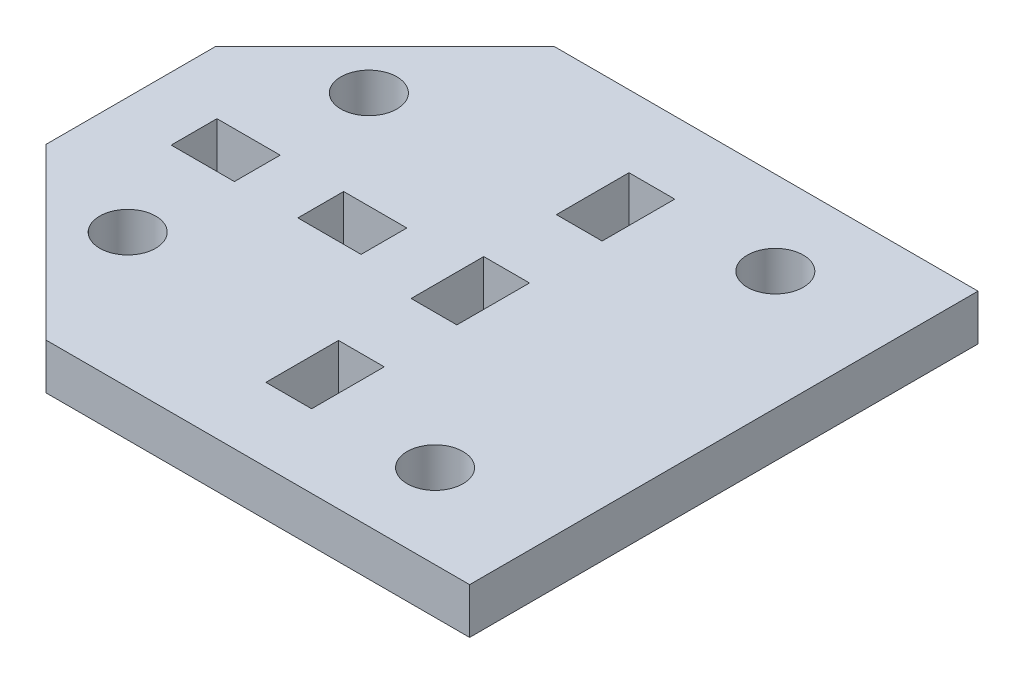
SolidWorks part; units mm, degrees
ref_plane "Ön Düzlem" through (0, 0, 0) normal (0, 0, 1) x (1, 0, 0)
ref_plane "Üst Düzlem" through (0, 0, 0) normal (0, 1, 0) x (1, 0, 0)
ref_plane "Sağ Düzlem" through (0, 0, 0) normal (1, 0, 0) x (0, 0, -1)
sketch "Sketch1" plane through (0, 0, 0) normal (0, 1, 0) x (1, 0, 0)
  line L0 (10.7767, -15.9461) -> (-9.2233, -15.9461)
  line L2 (10.7767, 14.0539) -> (-9.2233, 14.0539)
  line L4 (10.7767, -15.9461) -> (-9.2233, 14.0539) construction
  line L5 (10.7767, 14.0539) -> (-9.2233, -15.9461) construction
  line L14 (2.1267, -11.6204) -> (2.1267, -7.3347)
  line L16 (-19.2233, 4.0539) -> (-9.2233, 14.0539)
  line L17 (-9.2233, -15.9461) -> (-19.2233, -5.9461)
  line L18 (2.1267, -3.049) -> (2.1267, 1.2367)
  line L19 (-19.2233, 4.0539) -> (-19.2233, -5.9461)
  line L20 (2.1267, 5.5224) -> (2.1267, 9.8081)
  line L22 (-0.5733, -11.6204) -> (-0.5733, -7.3347)
  line L23 (10.7767, 14.0539) -> (15.7767, 14.0539)
  line L24 (-0.5733, -3.049) -> (-0.5733, 1.2367)
  line L26 (-0.5733, 5.5224) -> (-0.5733, 9.8081)
  line L27 (15.7767, 14.0539) -> (15.7767, -15.9461)
  line L28 (-0.5733, -11.6204) -> (2.1267, -11.6204)
  line L29 (-0.5733, -7.3347) -> (2.1267, -7.3347)
  line L30 (2.1267, -3.049) -> (-0.5733, -3.049)
  line L31 (-0.5733, 1.2367) -> (2.1267, 1.2367)
  line L32 (2.1267, 5.5224) -> (-0.5733, 5.5224)
  line L33 (-0.5733, 9.8081) -> (2.1267, 9.8081)
  line L34 (-15.4933, 0.4119) -> (-11.7633, 0.4119)
  line L35 (15.7767, -15.9461) -> (10.7767, -15.9461)
  line L36 (-8.0333, 0.4279) -> (-4.3033, 0.4279)
  line L38 (-15.4933, -2.2881) -> (-11.7633, -2.2881)
  line L40 (-8.0333, -2.2721) -> (-4.3033, -2.2721)
  line L42 (-15.4933, -2.2881) -> (-15.4933, 0.4119)
  line L43 (-11.7633, -2.2881) -> (-11.7633, 0.4119)
  line L44 (-8.0333, 0.4279) -> (-8.0333, -2.2721)
  line L45 (-4.3033, 0.4279) -> (-4.3033, -2.2721)
  circle A0 centre (-12.3262, -8.023) radius 1.65
  circle A2 centre (8.7767, 9.0938) radius 1.65
  circle A5 centre (-12.3262, 6.2107) radius 1.65
  circle A6 centre (8.7767, -10.9861) radius 1.65
  point P0 (0.7767, -0.9461)
  dimension "D1" = 30
  dimension "D2" = 20
extrude "Boss-Extrude1" add sketch "Sketch1" against normal blind 2.7
